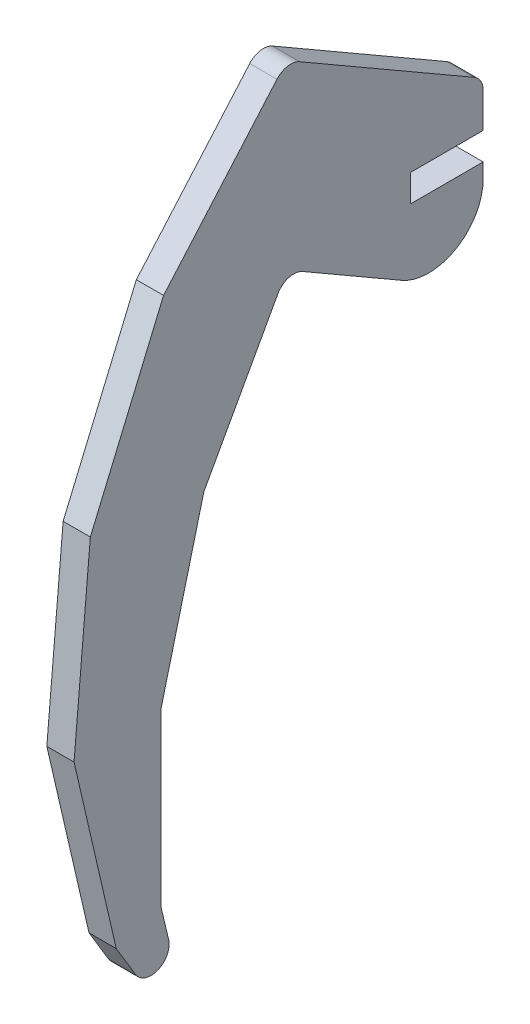
SolidWorks part; units mm, degrees
ref_plane "Front Plane" through (0, 0, 0) normal (0, 0, 1) x (1, 0, 0)
ref_plane "Top Plane" through (0, 0, 0) normal (0, 1, 0) x (1, 0, 0)
ref_plane "Right Plane" through (0, 0, 0) normal (1, 0, 0) x (0, 0, -1)
sketch "Sketch1" plane through (0, 0, 0) normal (1, 0, 0) x (0, 0, -1)
  line L0 (0, 0) -> (0, 20) construction
  line L1 (0, 0) -> (0, -70) construction
  line L2 (0, -70) -> (-10, -70) construction
  line L3 (-13.869, -53.8469) -> (-13.0192, -57.3951)
  line L4 (1.4281, 19.1755) -> (20.6506, 8.0774)
  line L5 (21.6506, -0.5) -> (21.6506, -2.1077)
  line L6 (21.6506, 6.3453) -> (21.6506, 2.5)
  line L7 (-0.9845, -1.7876) -> (-9.1328, -16.5827)
  line L8 (-1.0816, 18.7552) -> (-13.5801, 4.3705)
  line L9 (-13.5801, 4.3705) -> (-21.65, -14.6534)
  line L10 (-21.65, -14.6534) -> (-23.4462, -35.24)
  line L11 (-23.4462, -35.24) -> (-18.7929, -55.374)
  line L12 (-18.7929, -55.374) -> (-16.6782, -58.8915)
  line L13 (-9.1328, -16.5827) -> (-13.8547, -34.9156)
  line L14 (-13.8547, -34.9156) -> (-13.869, -53.8469)
  line L15 (12.6506, -7.3038) -> (1.7674, -1.0204)
  line L16 (21.6506, 2.5) -> (13.6506, 2.5)
  line L18 (21.6506, -0.5) -> (13.6506, -0.5)
  line L19 (13.6506, 2.5) -> (13.6506, -0.5)
  line L28 (58.4047, 33.4739) -> (48.1115, 34.372) [skipped]
  line L29 (37.8182, 35.2701) -> (27.7512, 32.9435) [skipped]
  line L30 (17.6842, 30.6168) -> (8.8289, 25.2932) [skipped]
  line L31 (77.4286, 25.4041) -> (67.9167, 29.439) [skipped]
  line L32 (93.0277, 11.8504) -> (85.2282, 18.6272) [skipped]
  line L33 (103.675, -5.8602) -> (98.3514, 2.9951) [skipped]
  line L34 (105.8571, -15.3019) -> (103.5305, -5.2349) [skipped]
  line L35 (0.0225, -80.1816) -> (7.822, -86.9584) [skipped]
  line L36 (7.4535, -86.6383) -> (16.9654, -90.6732) [skipped]
  line L37 (26.4774, -94.7081) -> (36.7707, -95.6062) [skipped]
  line L38 (57.9453, -93.9895) -> (68.0123, -91.6628) [skipped]
  line L39 (76.8103, -86.0723) -> (85.6657, -80.7486) [skipped]
  line L40 (92.2664, -72.7356) -> (99.0432, -64.936) [skipped]
  line L41 (98.4622, -65.6047) -> (102.4972, -56.0927) [skipped]
  line L42 (106.5321, -46.5808) -> (107.4302, -36.2875) [skipped]
  line L66 (28.9617, 23.9222) -> (20.9657, 18.8564) [skipped]
  line L67 (46.9708, 29.7587) -> (37.9663, 26.8405) [skipped]
  line L68 (65.8656, 30.9331) -> (56.4182, 30.3459) [skipped]
  line L69 (84.4589, 27.3716) -> (75.1623, 29.1523) [skipped]
  line L70 (116.1599, 7.2198) -> (108.8711, 13.2589) [skipped]
  line L71 (127.2759, -8.1044) -> (121.7179, -0.4423) [skipped]
  line L72 (134.2316, -25.7115) -> (127.2759, -8.1044) [skipped]
  line L73 (136.5901, -44.4953) -> (134.2316, -25.7115) [skipped]
  line L74 (101.5823, 19.2981) -> (93.0206, 23.3348) [skipped]
  line L75 (134.2031, -63.2755) -> (135.3966, -53.8854) [skipped]
  line L76 (20.8698, -107.6716) -> (28.8581, -112.7496) [skipped]
  line L77 (75.0507, -118.0497) -> (84.35, -116.2831) [skipped]
  line L78 (92.9178, -112.2593) -> (101.4856, -108.2355) [skipped]
  line L79 (108.7836, -102.2074) -> (116.0816, -96.1793) [skipped]
  line L80 (116.0816, -96.1793) -> (127.2207, -80.872) [skipped]
  line L81 (130.7119, -72.0738) -> (134.2031, -63.2755) [skipped]
  line L82 (46.8584, -118.6133) -> (56.3049, -119.2148) [skipped]
  line L83 (37.8582, -115.6815) -> (46.8584, -118.6133) [skipped]
  line L84 (-0.0673, -88.7835) -> (6.4071, -95.6885) [skipped]
  line L85 (-9.1749, -72.187) -> (-4.6211, -80.4852) [skipped]
  line L86 (-13.869, -53.8469) -> (-11.522, -63.0169) [skipped]
  line L87 (9.0855, 9.6604) -> (6.4849, 6.8952) [skipped]
  arc A0 (21.6506, -2.1077) -> (12.6506, -7.3038) centre (15.6506, -2.1077) cw
  arc A1 (20.6506, 8.0774) -> (21.6506, 6.3453) centre (19.6506, 6.3453) cw
  arc A2 (-13.0192, -57.3951) -> (-16.6782, -58.8915) centre (-14.9641, -57.861) cw
  arc A3 (-0.9845, -1.7876) -> (1.7674, -1.0204) centre (0.7674, -2.7524) cw
  arc A4 (1.4281, 19.1755) -> (-1.0816, 18.7552) centre (0.4281, 17.4434) ccw
  point P18 (21.6506, -12.5)
  point P19 (21.6506, -12.5)
  point P23 (21.6506, 7.5)
  dimension "D3" = 6
  dimension "D1" = 20
  dimension "D2" = 70
  dimension "D4" = 10
  dimension "D5" = 20
  dimension "D6" = 8
  dimension "D7" = 3
  dimension "D8" = 5
extrude "Boss-Extrude1" add sketch "Sketch1" along normal blind 3
